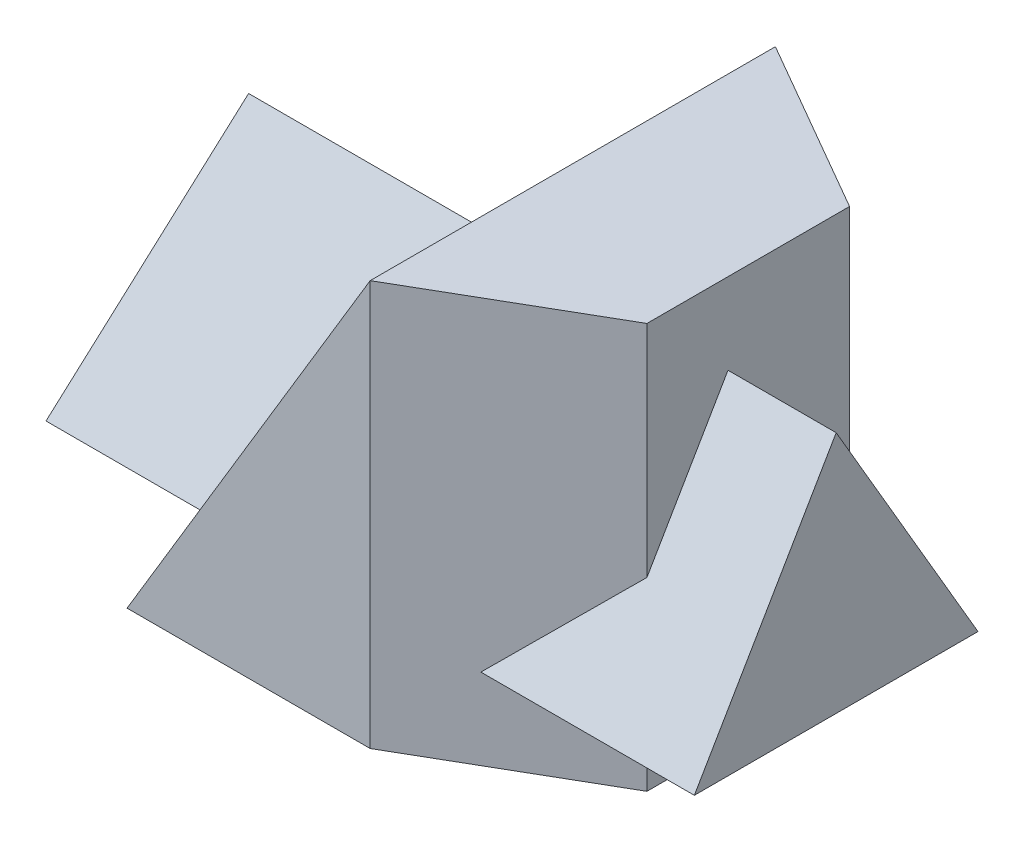
SolidWorks part; units mm, degrees
ref_plane "Front Plane" through (0, 0, 0) normal (0, 0, 1) x (1, 0, 0)
ref_plane "Top Plane" through (0, 0, 0) normal (0, 1, 0) x (1, 0, 0)
ref_plane "Right Plane" through (0, 0, 0) normal (1, 0, 0) x (0, 0, -1)
sketch "Sketch1" plane through (0, 0, 0) normal (0, 1, 0) x (1, 0, 0)
  line L0 (60, 0) -> (103.3013, 25)
  line L1 (0, 0) -> (60, 0)
  line L2 (0, 0) -> (0, 100)
  line L3 (0, 100) -> (60, 100)
  line L4 (60, 0) -> (60, 100) construction
  line L5 (103.3013, 25) -> (103.3013, 75)
  line L6 (103.3013, 75) -> (60, 100)
  dimension "D1" = 60
  dimension "D2" = 100
  dimension "D3" = 60
  dimension "D4" = 60
  dimension "D5" = 50
extrude "Extrude1" add sketch "Sketch1" along normal blind 100
sketch "Sketch2" plane through (0, 0, 0) normal (0, 0, 1) x (1, 0, 0)
  line L0 (60, 100) -> (0, 0)
  line L1 (0, 0) -> (0, 100)
  line L2 (0, 100) -> (60, 100)
extrude "Extrude2" cut sketch "Sketch2" against normal through all
sketch "Sketch3" plane through (0, 0, 0) normal (1, 0, 0) x (0, 0, -1)
  line L0 (45, 80) -> (80, 20)
  line L1 (80, 20) -> (10, 20)
  line L2 (10, 20) -> (45, 80)
  line L3 (25, 0) -> (75, 0) construction
  line L4 (100, 100) -> (100, 0) construction
  dimension "D1" = 70
  dimension "D2" = 35
  dimension "D3" = 60
  dimension "D4" = 20
  dimension "D5" = 20
extrude "Extrude3" add sketch "Sketch3" along normal blind 160 from offset 30
sketch "Sketch4" plane through (0, 0, 0) normal (0, 0, 1) x (1, 0, 0)
  line L0 (-30, 20) -> (-15, 80)
  line L1 (48, 80) -> (-30, 80) construction
  line L2 (-15, 80) -> (-30, 80)
  line L3 (-30, 80) -> (-30, 20)
  dimension "D1" = 15
extrude "Extrude4" cut sketch "Sketch4" against normal blind 160
